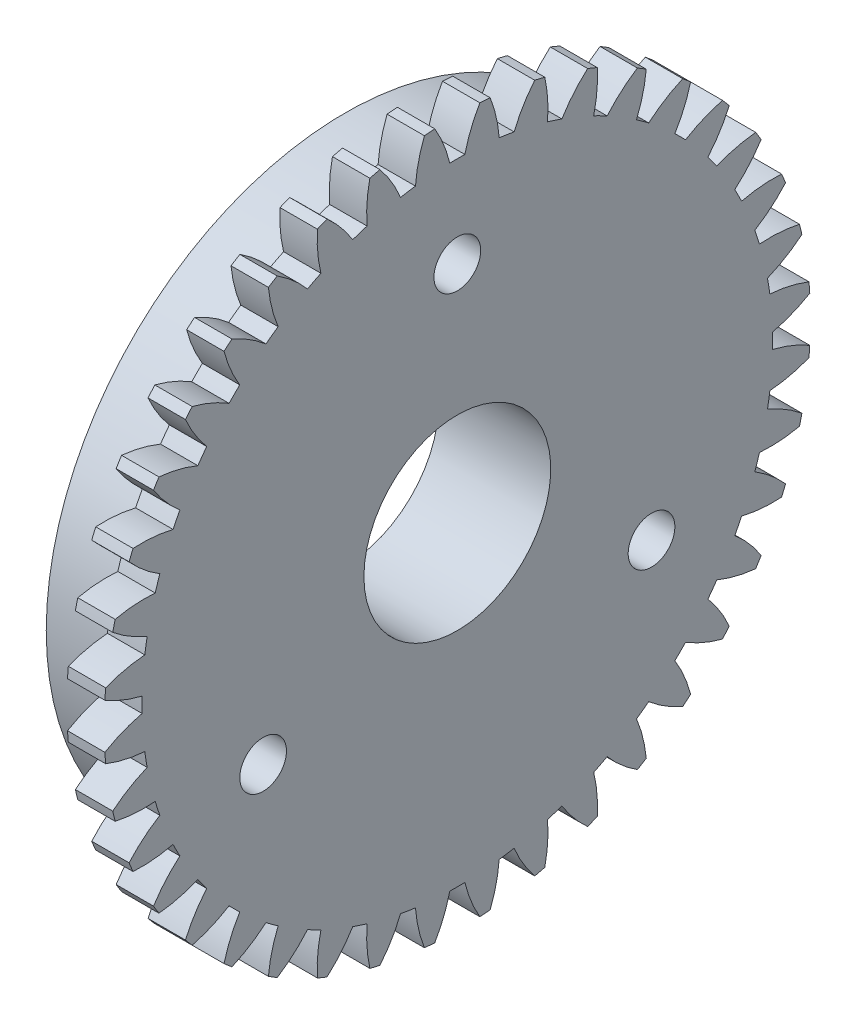
SolidWorks part; units mm, degrees
ref_plane "Plane1" through (0, 0, 0) normal (0, 0, 1) x (1, 0, 0)
ref_plane "Plane2" through (0, 0, 0) normal (0, 1, 0) x (1, 0, 0)
ref_plane "Plane3" through (0, 0, 0) normal (1, 0, 0) x (0, 0, -1)
sketch "HoldingSke" plane through (0, 0, 0) normal (0, 1, 0) x (1, 0, 0)
  line L0 (0, 0) -> (0.8512, -0.7142)
  line L1 (-15, 0) -> (100, 0) construction
  line L2 (0, 0) -> (-2.1039, 2.3779)
  line L3 (0, 0) -> (-11.863, 4.5341)
  line L4 (0, 0) -> (6.6156, 5.5511)
  line L5 (0, 0) -> (-5.6217, -2.0967)
  line L6 (0, 0) -> (-1.6579, -1.1186)
  line L7 (-2.1039, 2.3779) -> (-0.8124, 8.2373)
  line L8 (-76.2, 54.61) -> (-75.2, 54.61)
  line L9 (-71.009, 38.7566) -> (-53.1078, 45.2721)
  line L10 (-76.2, 71.12) -> (104.1128, 71.12)
  line L11 (0, 0) -> (-2, 0)
  line L12 (-76.2, 101.6) -> (-76.166, 101.6)
  line L13 (24.9733, 27.94) -> (52.9518, 28.4284)
  line L14 (24.9733, 27.94) -> (24.9743, 27.94)
  line L15 (24.9733, 27.94) -> (100.4006, 29.5858)
  line L16 (-63.627, -0.9) -> (-12.827, -0.9)
  circle A0 centre (0, 0) radius 3
  circle A1 centre (0, 0) radius 16
  circle A2 centre (0, 0) radius 16
  circle A3 centre (0, 0) radius 3
  dimension "MHD" = 32
  dimension "Hub_dia" = 32
  dimension "Bore" = 6
  dimension "MBD" = 6
  dimension "Num_teeth" = 40
  dimension "Pitch_radius" = 180.3128
  dimension "Pitch" = 1.1111
  dimension "Width" = 2
  dimension "Overall_len" = 6
  dimension "Show_teeth" = 40
  dimension "Thickness" = 2
  dimension "OAL" = 6.0001
  dimension "T_dim" = 1
  dimension "Ap" = 20
  dimension "H" = 19.05
  dimension "Backlash" = 0.034
  dimension "Addendum_fac" = 1
  dimension "Dedendum_fac" = 1.25
  dimension "Clearance_fac" = 0.25
  dimension "Dedendum_add" = 0.001
  dimension "Module" = 0.9
sketch "BasProSke" plane through (0, 0, 0) normal (0, 1, 0) x (1, 0, 0)
  line L0 (-10, 0) -> (60, 0) construction
  line L1 (0, 0) -> (0, 18.9)
  line L2 (0, 0) -> (2, 0)
  line L3 (2, 0) -> (2, 18.9)
  line L4 (2, 18.9) -> (0, 18.9)
  dimension "Diameter" = 37.8
  dimension "Thickness" = 2
revolve "Base-Revolve" add sketch "BasProSke" angle 360 about L0
sketch "TooCutSke" plane through (0, 0, 0) normal (1, 0, 0) x (0, 0, -1)
  line L1 (0, 0) -> (0, 107) construction
  line L2 (0, 0) -> (-0.7662, 17.9837) construction
  line L3 (0, 0) -> (-2.8227, 35.8658) construction
  line L4 (-0.7662, 17.9837) -> (-1.4114, 17.9329) construction
  arc A0 (0.4035, 16.8692) -> (-0.4035, 16.8692) centre (0, 0) ccw
  arc A1 (1.2204, 18.886) -> (-1.2204, 18.886) centre (0, 0) ccw
  circle A2 centre (0, 0) radius 18 construction
  circle A3 centre (0, 0) radius 16.9145 construction
  arc A4 (-0.4035, 16.8692) -> (-1.2204, 18.886) centre (-7.4086, 15.2056) ccw
  arc A5 (1.2204, 18.886) -> (0.4035, 16.8692) centre (7.4086, 15.2056) ccw
  dimension "Root_dia" = 33.748
  dimension "Overcut_dia" = 37.8508
  dimension "Pitch_dia" = 36
  dimension "Base_dia" = 33.8289
  dimension "Flank_rad" = 7.2
  dimension "Half_ang" = 4.5
  dimension "Half_CT" = 0.6472
extrude "ToothCut" cut sketch "TooCutSke" along normal through all
fillet "Breaks" [suppressed] radius 0.018
fillet "RootFillets" [suppressed] radius 0.226
pattern_circular "TeethCuts" count 40 every 9 about axis through (-10, 0, 0) along (1, 0, 0) of "ToothCut", "RootFillets", "Breaks"
sketch "HubNeaOneSke" plane through (0, 0, 0) normal (-1, 0, 0) x (0, 0, 1)
  circle A0 centre (0, 0) radius 16
  dimension "Diameter" = 32
extrude "HubNearOne" add sketch "HubNeaOneSke" along normal blind 4.0001
sketch "HubNeaBotSke" plane through (0, 0, 0) normal (-1, 0, 0) x (0, 0, 1)
  circle A0 centre (0, 0) radius 16
  dimension "Diameter" = 32
extrude "HubNearBoth" [suppressed] add sketch "HubNeaBotSke" along normal blind 2
ref_plane "FarPln" through (2, 0, 0) normal (1, 0, 0) x (0, 0, -1)
sketch "HubFarSke" plane through (2, 0, 0) normal (1, 0, 0) x (0, 0, -1)
  circle A0 centre (0, 0) radius 16
  dimension "Diameter" = 32
extrude "HubFar" [suppressed] add sketch "HubFarSke" along normal blind 2
sketch "BorSke" plane through (0, 0, 0) normal (1, 0, 0) x (0, 0, -1)
  circle A0 centre (0, 0) radius 3
  dimension "Diameter" = 6
extrude "Bore" cut sketch "BorSke" along normal mid plane 12.0001
sketch "KeySke" plane through (0, 0, 0) normal (1, 0, 0) x (0, 0, -1)
  line L0 (-1, 0) -> (-1, 4)
  line L1 (-1, 4) -> (1, 4)
  line L2 (1, 4) -> (1, 0)
  line L3 (0, 0) -> (0, 34) construction
  line L4 (-1, 0) -> (1, 0)
  dimension "Offset" = 4
  dimension "Width" = 2
extrude "Keyway" [suppressed] cut sketch "KeySke" along normal mid plane 12.0001
pattern_circular "Keyway2" [suppressed] count 2 every 90 about axis through (-10, 0, 0) along (1, 0, 0)
sketch "Sketch1" plane through (-4.0001, 0, 0) normal (-1, 0, 0) x (0, 0, 1)
  circle A0 centre (0, 0) radius 5
extrude "Cut-Extrude1" cut sketch "Sketch1" against normal through all
sketch "Sketch3" plane through (-4.0001, 0, 0) normal (-1, 0, 0) x (0, 0, 1)
  line L0 (0, 0) -> (0, 12) construction
  line L1 (0, 0) -> (-10.3923, -6) construction
  line L2 (0, 0) -> (10.3923, -6) construction
hole_wizard "Ø2.5mm Dowel Hole1" positions "Sketch6" profile "Sketch5" hole size "Ø2.5" standard "ANSI Metric"
sketch "Sketch6" plane through (-4.0001, 0, 0) normal (-1, 0, 0) x (0, 0, 1)
  point P0 (0, 12)
  point P3 (10.3923, -6)
  point P6 (-10.3923, -6)
sketch "Sketch5" plane through (-4.0001, 12, 0) normal (0, 1, 0) x (0, 0, 1)
  line L0 (0, 0) -> (0, 10.7511)
  line L1 (0, 10.7511) -> (1.25, 10)
  line L2 (1.25, 10) -> (1.25, 0)
  line L5 (1.25, 0) -> (0, 0)
  line L10 (0, 10.7511) -> (-1.25, 10) construction
  line L11 (0, -6.35) -> (0, 107.95) construction
  dimension "Hole Dia." = 2.5
  dimension "Hole Depth" = 10
  dimension "Drill Angle" = 118
equation "' \"Module@HoldingSke\" = 6.35"
equation "' \"Num_teeth@HoldingSke\" = 12"
equation "' \"Ap@HoldingSke\" =  20"
equation "' \"Width@HoldingSke\" = 0.5 * 25.4"
equation "' \"Hub_dia@HoldingSke\"= 1 * 25.4"
equation "' \"Overall_len@HoldingSke\" = 1.0 * 25.4"
equation "' \"Bore@HoldingSke\" = 0.75 * 25.4"
equation "' \"T_dim@HoldingSke\" = 0.1 * 25.4"
equation "' \"Width@KeySke\" = 0.25 * 25.4"
equation "' \"Show_teeth@HoldingSke\" = 13"
equation "' \"Backlash@HoldingSke\" = 0.009 * 25.4"
equation "' \"Addendum_fac@HoldingSke\" = 1.0"
equation "' \"Dedendum_fac@HoldingSke\" = 1.25"
equation "' \"Dedendum_add@HoldingSke\" = 0.00005 * 25.4"
equation "' \"Clearance_fac@HoldingSke\" = 0.25"
equation "\"Pitch@HoldingSke\" = 1 / \"Module@HoldingSke\""
equation "\"Overcut_dia@TooCutSke\" = (\"Num_teeth@HoldingSke\" + 2 * \"Addendum_fac@HoldingSke\") / \"Pitch@HoldingSke\" + 0.002 * 25.4"
equation "\"Pitch_dia@TooCutSke\" = \"Num_teeth@HoldingSke\" / \"Pitch@HoldingSke\""
equation "\"Base_dia@TooCutSke\" = \"Num_teeth@HoldingSke\" / \"Pitch@HoldingSke\" * cos((\"Ap@HoldingSke\"  * 3.14159265 / 180))"
equation "\"Root_dia@TooCutSke\" = (\"Num_teeth@HoldingSke\" + 2) / \"Pitch@HoldingSke\" - 2 * (\"Addendum_fac@HoldingSke\" + \"Dedendum_fac@HoldingSke\") / \"Pitch@HoldingSke\" - \"Dedendum_add@HoldingSke\" * 2"
equation "\"Half_ang@TooCutSke\" = 180 / \"Num_teeth@HoldingSke\""
equation "\"Half_CT@TooCutSke\" = \"Num_teeth@HoldingSke\" / \"Pitch@HoldingSke\" * sin((3.14159265 / 2 / \"Num_teeth@HoldingSke\")) / 2 - 7 * \"Backlash@HoldingSke\" / 4"
equation "\"Flank_rad@TooCutSke\" = \"Num_teeth@HoldingSke\" / \"Pitch@HoldingSke\" / 5"
equation "\"Radius@RootFillets\" = \"Clearance_fac@HoldingSke\" / \"Pitch@HoldingSke\" + \"Dedendum_add@HoldingSke\""
equation "\"Break_rad@Breaks\" = 0.02 / \"Pitch@HoldingSke\""
equation "\"Thickness@HoldingSke\" = \"Width@HoldingSke\""
equation "\"OAL@HoldingSke\" = \"Thickness@HoldingSke\""
equation "\"MHD@HoldingSke\" = (\"Num_teeth@HoldingSke\" + 2) / \"Pitch@HoldingSke\" - 2 * (\"Addendum_fac@HoldingSke\" + \"Dedendum_fac@HoldingSke\")  / \"Pitch@HoldingSke\" - \"Dedendum_add@HoldingSke\" * 2"
equation "\"MBD@HoldingSke\" = (\"Num_teeth@HoldingSke\" + 2) / \"Pitch@HoldingSke\" - 2 * (\"Addendum_fac@HoldingSke\" + \"Dedendum_fac@HoldingSke\")  / \"Pitch@HoldingSke\" - \"Dedendum_add@HoldingSke\" * 2 - 0.002 * 25.4"
equation "\"MHD@HoldingSke\" = ((sgn( \"MHD@HoldingSke\" - \"Hub_dia@HoldingSke\" )-1)*( \"MHD@HoldingSke\" - \"Hub_dia@HoldingSke\" ))/-2+ \"Hub_dia@HoldingSke\""
equation "\"MBD@HoldingSke\" = ((sgn( \"MBD@HoldingSke\" - \"Bore@HoldingSke\" )-1)*( \"MBD@HoldingSke\" - \"Bore@HoldingSke\" ))/-2+ \"Bore@HoldingSke\""
equation "\"OAL@HoldingSke\" = ((sgn( \"OAL@HoldingSke\" - \"Overall_len@HoldingSke\" )+1)*( \"OAL@HoldingSke\" - \"Overall_len@HoldingSke\" ))/2 + \"Overall_len@HoldingSke\" + 0.000002 * 25.4"
equation "\"Num_teeth@TeethCuts\" = int( \"Show_teeth@HoldingSke\" ) + 1"
equation "\"Num_teeth@TeethCuts\" = ((sgn( \"Num_teeth@TeethCuts\" - \"Num_teeth@HoldingSke\" )-1)*( \"Num_teeth@TeethCuts\" - \"Num_teeth@HoldingSke\" ))/-2+ \"Num_teeth@HoldingSke\""
equation "\"Num_teeth@TeethCuts\" = ((sgn( \"Num_teeth@TeethCuts\" - 2.0)+1)*( \"Num_teeth@TeethCuts\" - 2.0))/2 +2.0"
equation "\"Angle@TeethCuts\" = 360.0 / \"Num_teeth@HoldingSke\""
equation "\"Diameter@BasProSke\" = (\"Num_teeth@HoldingSke\" + 2 * \"Addendum_fac@HoldingSke\") / \"Pitch@HoldingSke\""
equation "\"Thickness@BasProSke\"  = \"Thickness@HoldingSke\""
equation "' \"Fillet_rad@BasProSke\" =  \"Thickness@HoldingSke\" * 0.05"
equation "\"MHD@HoldingSke\" = ((sgn( \"MHD@HoldingSke\" - \"Root_dia@TooCutSke\" )-1)*( \"MHD@HoldingSke\" - \"Root_dia@TooCutSke\" ))/-2+ \"Root_dia@TooCutSke\""
equation "\"Diameter@HubNeaOneSke\" = \"MHD@HoldingSke\""
equation "\"Length@HubNearOne\" = \"OAL@HoldingSke\" - \"Thickness@BasProSke\""
equation "\"Diameter@HubNeaBotSke\" = \"MHD@HoldingSke\""
equation "\"Length@HubNearBoth\" = ( \"OAL@HoldingSke\" - \"Thickness@BasProSke\" ) / 2.0"
equation "\"Thickness@FarPln\" = \"Thickness@BasProSke\""
equation "\"Diameter@HubFarSke\" = \"MHD@HoldingSke\""
equation "\"Length@HubFar\" = ( \"OAL@HoldingSke\" - \"Thickness@BasProSke\" ) / 2.0"
equation "\"Diameter@BorSke\" = \"MBD@HoldingSke\""
equation "\"D1@Bore\" = \"OAL@HoldingSke\" * 2.0"
equation "\"D1@Keyway\" = \"OAL@HoldingSke\" * 2.0"
equation "\"Offset@KeySke\" = \"T_dim@HoldingSke\" + \"MBD@HoldingSke\" / 2.0"
